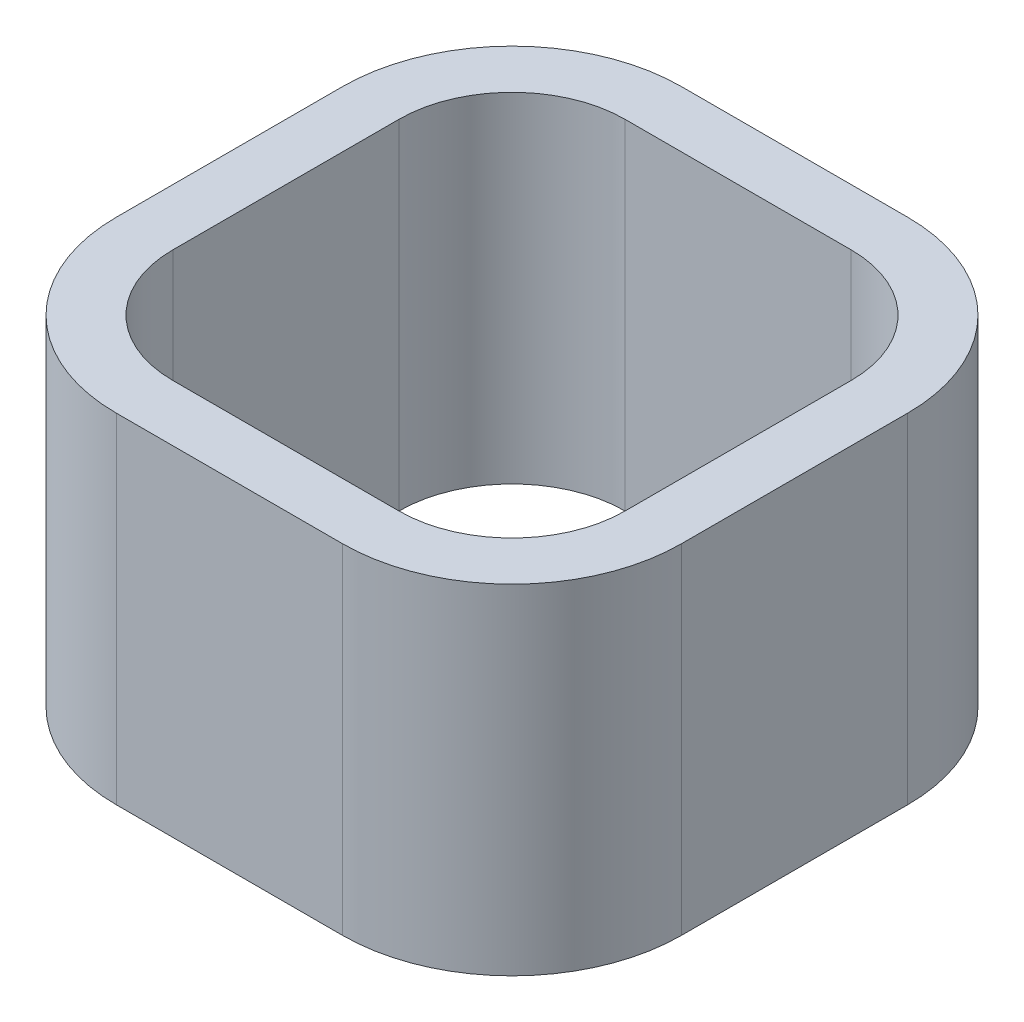
SolidWorks part; units mm, degrees
ref_plane "Ebene vorne" through (0, 0, 0) normal (0, 0, 1) x (1, 0, 0)
ref_plane "Ebene oben" through (0, 0, 0) normal (0, 1, 0) x (1, 0, 0)
ref_plane "Ebene rechts" through (0, 0, 0) normal (1, 0, 0) x (0, 0, -1)
sketch "Skizze1" plane through (0, 0, 0) normal (0, 1, 0) x (1, 0, 0)
  line L0 (-2, 2) -> (2, 2)
  line L1 (-2, 2) -> (-2, -2)
  line L2 (-2, -2) -> (2, -2)
  line L3 (2, 2) -> (2, -2)
  line L4 (-2, 2) -> (2, -2) construction
  line L5 (-2, -2) -> (2, 2) construction
  line L6 (-2.5, 2.5) -> (2.5, 2.5)
  line L7 (-2.5, 2.5) -> (-2.5, -2.5)
  line L8 (-2.5, -2.5) -> (2.5, -2.5)
  line L9 (2.5, 2.5) -> (2.5, -2.5)
  line L10 (-2.5, 2.5) -> (2.5, -2.5) construction
  line L11 (-2.5, -2.5) -> (2.5, 2.5) construction
  point P0 (0, 0)
  point P5 (0, 0)
  dimension "D1" = 4
  dimension "D2" = 4
  dimension "D3" = 5
  dimension "D4" = 5
extrude "Aufsatz-Linear austragen1" add sketch "Skizze1" along normal blind 3
fillet "Verrundung1" radius 1 4 edges at (-2, 1.5, 2) (2, 1.5, 2) (2, 1.5, -2) (-2, 1.5, -2)
fillet "Verrundung2" radius 1.5 4 edges at (2.5, 1.5, 2.5) (-2.5, 1.5, 2.5) (-2.5, 1.5, -2.5) (2.5, 1.5, -2.5)
sketch "Skizze2" plane through (0, 0, 0) normal (0, 1, 0) x (1, 0, 0)
  line L0 (0, 0) -> (0, 4.1213) construction
  line L1 (0, 4.1213) -> (-3.0576, 1.0638) construction
  arc A0 (-1, 2.5) -> (-2.5, 1) centre (-1, 1) ccw construction
  dimension "D1" = 45
ref_plane "Ebene1" through (-2.0607, 0, -2.0607) normal (-0.7071, 0, -0.7071) x (-0.7071, 0, 0.7071)
sketch "Skizze3" plane through (-2.0607, 0, -2.0607) normal (-0.7071, 0, -0.7071) x (-0.7071, 0, 0.7071)
  line L1 (-1.0607, 0) -> (1.0607, 0) construction
  line L2 (-2.9142, 0) -> (1.4098, 0) construction
  line L3 (1.0607, 3) -> (-1.0607, 3) construction
  point P0 (0, 1.5)
  point P7 (0, 3)
  dimension "D1" = 1.5
  dimension "D2" = 1.5
  dimension "D3" = 1.5
hole_wizard "Ø0.3 (0.3) Durchmesser Bohrung3" positions "Skizze9" profile "Skizze10" hole size "Ø0.3" standard "DIN"
sketch "Skizze9" plane through (-2.0607, 0, -2.0607) normal (-0.7071, 0, -0.7071) x (-0.7071, 0, 0.7071)
  point P0 (0, 1.5)
sketch "Skizze10" plane through (-2.0607, 1.5, -2.0607) normal (0, 1, 0) x (-0.7071, 0, 0.7071)
  line L0 (0, 0) -> (0, 0.16)
  line L1 (0, 0.16) -> (0.15, 0.01)
  line L2 (0.15, 0.01) -> (0.15, 0)
  line L5 (0.15, 0) -> (0, 0)
  line L10 (0, 0.16) -> (-0.15, 0.01) construction
  line L11 (0, -6.35) -> (0, 107.95) construction
  dimension "Bohrerdurchmesser" = 0.3
  dimension "Bohrungstiefe" = 0.01
  dimension "Spitzenwinkel" = 90
